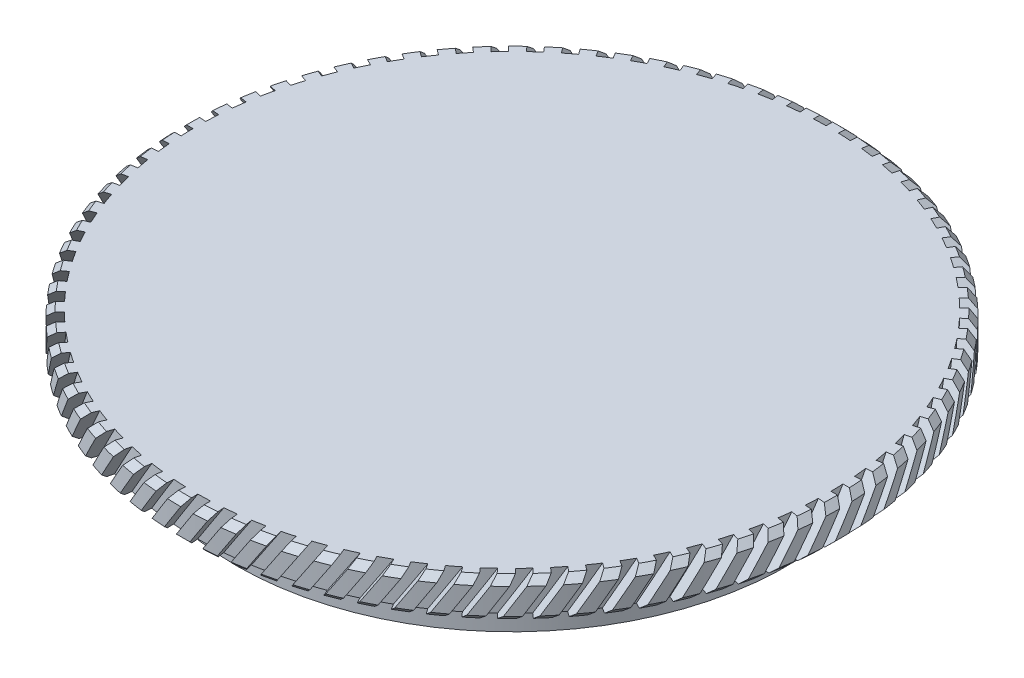
SolidWorks part; units mm, degrees
ref_plane "前视基准面" through (0, 0, 0) normal (0, 0, 1) x (1, 0, 0)
ref_plane "上视基准面" through (0, 0, 0) normal (0, 1, 0) x (1, 0, 0)
ref_plane "右视基准面" through (0, 0, 0) normal (1, 0, 0) x (0, 0, -1)
sketch "草图1" plane through (0, 0, 0) normal (0, 0, 1) x (1, 0, 0)
  line L0 (0, 66.6288) -> (0, -106.6399) construction
  line L1 (-97.6622, 0) -> (93.4292, 0) construction
  line L2 (0, 21.8713) -> (25.4, 21.8713)
  line L3 (25.4, 21.8713) -> (25.4, 18.8713)
  line L4 (20.5, 18.8713) -> (20.5, 17.8713)
  line L5 (20.5, 18.8713) -> (25.4, 18.8713)
  line L6 (21.2, 17.8713) -> (21.2, 15.3713)
  line L7 (20.5, 17.8713) -> (21.2, 17.8713)
  line L8 (16, 18.8713) -> (16, 15.3713)
  line L9 (0, 21.8713) -> (0, 18.8713)
  line L10 (16, 15.3713) -> (21.2, 15.3713)
  line L11 (0, 18.8713) -> (16, 18.8713)
  dimension "D1" = 25.4
  dimension "D2" = 3
  dimension "D3" = 20.5
  dimension "D4" = 21.2
  dimension "D5" = 16
  dimension "D6" = 1
  dimension "D7" = 2.5
revolve "旋转2" add sketch "草图1" angle 360 about L0
cosmetic thread "装饰螺纹线1" parameters "D2"=38
chamfer "倒角1" distance 0.5 angle 45 2 edges at (0, 21.8713, 25.4) (0, 18.8713, 25.4)
sketch "草图2" plane through (0, 0, 0) normal (0, 0, 1) x (1, 0, 0)
  line L0 (1.1082, 23.3033) -> (-5.3395, 13.2735)
  line L1 (1.1082, 23.3033) -> (1.7811, 22.8706)
  line L2 (-5.3395, 13.2735) -> (-4.6666, 12.8409)
  line L3 (1.7811, 22.8706) -> (-4.6666, 12.8409)
  dimension "D1" = 0.8
surface "曲面-等距1" parameters "D1"=1
extrude "切除-拉伸1" cut sketch "草图2" against normal up to surface (5.6252 mm away) from offset 30
delete or keep bodies "实体-删除/保留 1" type delete bodies bodies 107
pattern_circular "阵列(圆周)2" count 80 over 360 about axis through (0, 0, 0) along (0, 1, 0) of "切除-拉伸1"
